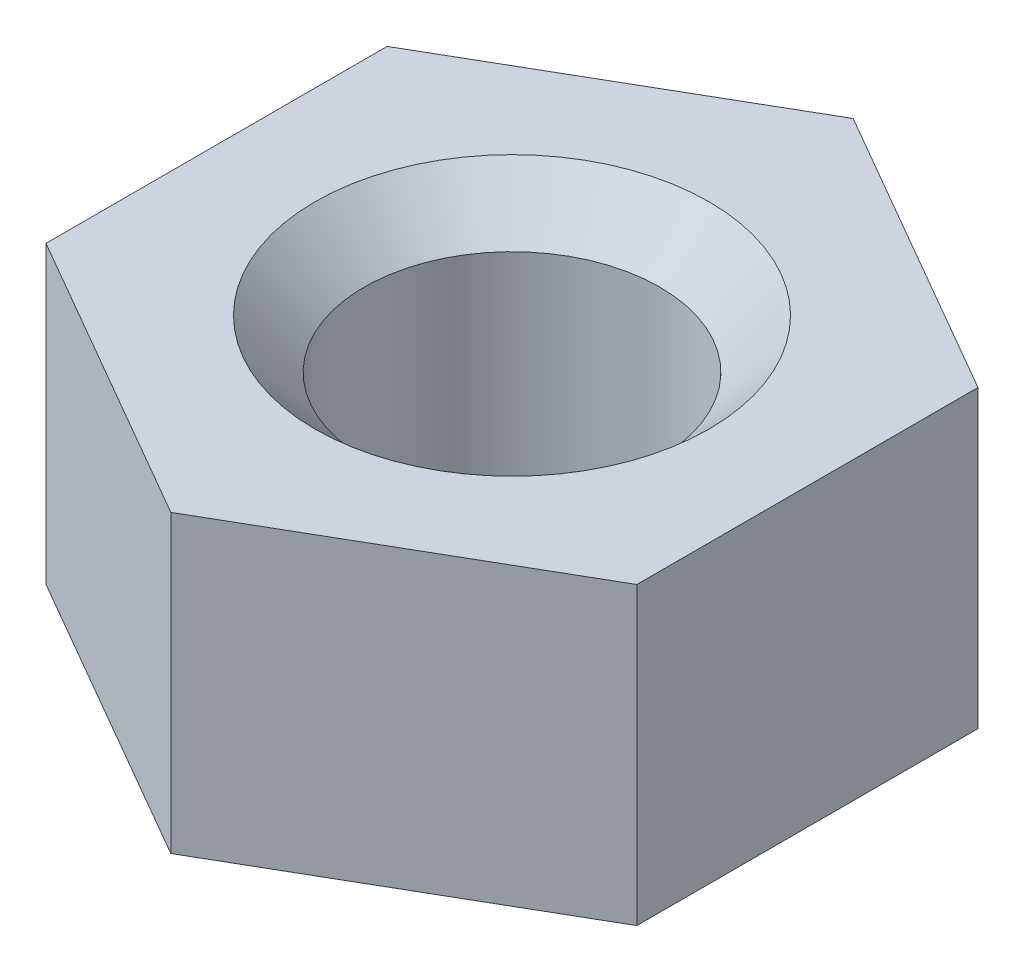
SolidWorks part; units mm, degrees
ref_plane "Front Plane" through (0, 0, 0) normal (0, 0, 1) x (1, 0, 0)
ref_plane "Top Plane" through (0, 0, 0) normal (0, 1, 0) x (1, 0, 0)
ref_plane "Right Plane" through (0, 0, 0) normal (1, 0, 0) x (0, 0, -1)
sketch "Sketch1" plane through (0, 0, 0) normal (0, 1, 0) x (1, 0, 0)
  line L1 (0, 6.9282) -> (-6, 3.4641)
  line L2 (-6, 3.4641) -> (-6, -3.4641)
  line L3 (-6, -3.4641) -> (0, -6.9282)
  line L4 (0, -6.9282) -> (6, -3.4641)
  line L5 (6, -3.4641) -> (6, 3.4641)
  line L6 (6, 3.4641) -> (0, 6.9282)
  circle A0 centre (0, 0) radius 6 construction
  dimension "D1" = 12
extrude "Boss-Extrude1" add sketch "Sketch1" along normal blind 6
sketch "Sketch2" plane through (0, 6, 0) normal (0, 1, 0) x (1, 0, 0)
  circle A0 centre (0, 0) radius 3
  dimension "D1" = 6
extrude "Cut-Extrude1" cut sketch "Sketch2" against normal blind 6
chamfer "Chamfer2" distance 1 angle 45 2 edges at (0, 6, 3) (0, 0, 3)
